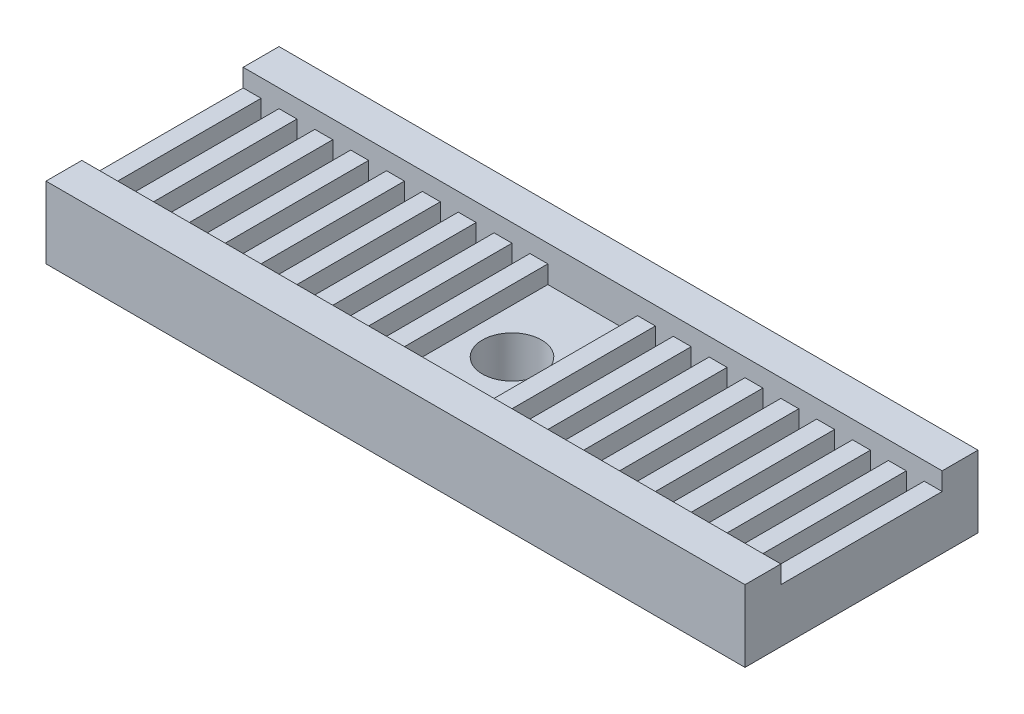
SolidWorks part; units mm, degrees
ref_plane "Front Plane" through (0, 0, 0) normal (0, 0, 1) x (1, 0, 0)
ref_plane "Top Plane" through (0, 0, 0) normal (0, 1, 0) x (1, 0, 0)
ref_plane "Right Plane" through (0, 0, 0) normal (1, 0, 0) x (0, 0, -1)
sketch "Sketch1" plane through (0, 0, 0) normal (0, 1, 0) x (1, 0, 0)
  line L5 (-19.5, -6.5) -> (19.5, -6.5)
  line L6 (-19.5, -6.5) -> (-19.5, 6.5)
  line L15 (-19.5, 6.5) -> (19.5, 6.5)
  line L16 (19.5, -6.5) -> (19.5, 6.5)
  line L17 (-19.5, -6.5) -> (19.5, 6.5) construction
  line L18 (-19.5, 6.5) -> (19.5, -6.5) construction
  point P0 (0, 0)
  dimension "D1" = 13
  dimension "D2" = 39
extrude "Boss-Extrude1" add sketch "Sketch1" along normal blind 5
sketch "Sketch5" plane through (0, 5, 0) normal (0, 1, 0) x (1, 0, 0)
  line L5 (19.5, -6.5) -> (19.5, 6.5) construction
  line L6 (-19.5, -4.5) -> (19.5, -4.5)
  line L8 (-19.5, -4.5) -> (-19.5, 4.5)
  line L9 (-19.5, 4.5) -> (19.5, 4.5)
  line L10 (19.5, -4.5) -> (19.5, 4.5)
  line L11 (-19.5, -4.5) -> (19.5, 4.5) construction
  line L12 (-19.5, 4.5) -> (19.5, -4.5) construction
  point P0 (0, 0)
  dimension "D1" = 9
extrude "Cut-Extrude1" cut sketch "Sketch5" against normal blind 2
sketch "Sketch2" plane through (0, 3, 0) normal (0, 1, 0) x (1, 0, 0)
  line L0 (-19.5, 0) -> (19.5, 0) construction
  line L1 (6.5, -4.5) -> (6.5, 4.5)
  line L2 (6.5, -4.5) -> (5.5, -4.5)
  line L3 (-17.5, -4.5) -> (-17.5, 4.5)
  line L4 (-18.5, -4.5) -> (-19.5, -4.5)
  line L5 (-18.5, -4.5) -> (-18.5, 4.5)
  line L6 (-18.5, 4.5) -> (-19.5, 4.5)
  line L7 (-19.5, -4.5) -> (-19.5, 4.5)
  line L8 (-18.5, -4.5) -> (-19.5, 4.5) construction
  line L9 (-18.5, 4.5) -> (-19.5, -4.5) construction
  line L10 (-17.5, -4.5) -> (-18.5, -4.5)
  line L11 (-18.5, -4.5) -> (-18.5, 4.5)
  line L12 (-17.5, 4.5) -> (-18.5, 4.5)
  line L13 (-16.5, -4.5) -> (-16.5, 4.5)
  line L14 (-16.5, -4.5) -> (-17.5, -4.5)
  line L15 (-17.5, -4.5) -> (-17.5, 4.5)
  line L16 (-16.5, 4.5) -> (-17.5, 4.5)
  line L17 (-15.5, -4.5) -> (-15.5, 4.5)
  line L18 (-15.5, -4.5) -> (-16.5, -4.5)
  line L19 (-16.5, -4.5) -> (-16.5, 4.5)
  line L20 (-15.5, 4.5) -> (-16.5, 4.5)
  line L21 (-14.5, -4.5) -> (-14.5, 4.5)
  line L22 (-14.5, -4.5) -> (-15.5, -4.5)
  line L23 (-15.5, -4.5) -> (-15.5, 4.5)
  line L24 (-14.5, 4.5) -> (-15.5, 4.5)
  line L25 (-13.5, -4.5) -> (-13.5, 4.5)
  line L26 (-13.5, -4.5) -> (-14.5, -4.5)
  line L27 (-14.5, -4.5) -> (-14.5, 4.5)
  line L28 (-13.5, 4.5) -> (-14.5, 4.5)
  line L29 (-12.5, -4.5) -> (-12.5, 4.5)
  line L30 (-12.5, -4.5) -> (-13.5, -4.5)
  line L31 (-13.5, -4.5) -> (-13.5, 4.5)
  line L32 (-12.5, 4.5) -> (-13.5, 4.5)
  line L33 (-11.5, -4.5) -> (-11.5, 4.5)
  line L34 (-11.5, -4.5) -> (-12.5, -4.5)
  line L35 (-12.5, -4.5) -> (-12.5, 4.5)
  line L36 (-11.5, 4.5) -> (-12.5, 4.5)
  line L37 (-10.5, -4.5) -> (-10.5, 4.5)
  line L38 (-10.5, -4.5) -> (-11.5, -4.5)
  line L39 (-11.5, -4.5) -> (-11.5, 4.5)
  line L40 (-10.5, 4.5) -> (-11.5, 4.5)
  line L41 (-9.5, -4.5) -> (-9.5, 4.5)
  line L42 (-9.5, -4.5) -> (-10.5, -4.5)
  line L43 (-10.5, -4.5) -> (-10.5, 4.5)
  line L44 (-9.5, 4.5) -> (-10.5, 4.5)
  line L45 (-8.5, -4.5) -> (-8.5, 4.5)
  line L46 (-8.5, -4.5) -> (-9.5, -4.5)
  line L47 (-9.5, -4.5) -> (-9.5, 4.5)
  line L48 (-8.5, 4.5) -> (-9.5, 4.5)
  line L49 (-7.5, -4.5) -> (-7.5, 4.5)
  line L50 (-7.5, -4.5) -> (-8.5, -4.5)
  line L51 (-8.5, -4.5) -> (-8.5, 4.5)
  line L52 (-7.5, 4.5) -> (-8.5, 4.5)
  line L53 (-6.5, -4.5) -> (-6.5, 4.5)
  line L54 (-6.5, -4.5) -> (-7.5, -4.5)
  line L55 (-7.5, -4.5) -> (-7.5, 4.5)
  line L56 (-6.5, 4.5) -> (-7.5, 4.5)
  line L57 (-5.5, -4.5) -> (-5.5, 4.5)
  line L58 (-5.5, -4.5) -> (-6.5, -4.5)
  line L59 (-6.5, -4.5) -> (-6.5, 4.5)
  line L60 (-5.5, 4.5) -> (-6.5, 4.5)
  line L61 (-4.5, -4.5) -> (-4.5, 4.5)
  line L62 (-4.5, -4.5) -> (-5.5, -4.5)
  line L63 (-5.5, -4.5) -> (-5.5, 4.5)
  line L64 (-4.5, 4.5) -> (-5.5, 4.5)
  line L65 (-3.5, -4.5) -> (-3.5, 4.5)
  line L66 (-3.5, -4.5) -> (-4.5, -4.5)
  line L67 (-4.5, -4.5) -> (-4.5, 4.5)
  line L68 (-3.5, 4.5) -> (-4.5, 4.5)
  line L69 (-2.5, -4.5) -> (-2.5, 4.5)
  line L70 (-2.5, -4.5) -> (-3.5, -4.5)
  line L71 (-3.5, -4.5) -> (-3.5, 4.5)
  line L72 (-2.5, 4.5) -> (-3.5, 4.5)
  line L73 (-1.5, -4.5) -> (-1.5, 4.5)
  line L74 (-1.5, -4.5) -> (-2.5, -4.5)
  line L75 (-2.5, -4.5) -> (-2.5, 4.5)
  line L76 (-1.5, 4.5) -> (-2.5, 4.5)
  line L77 (-0.5, -4.5) -> (-0.5, 4.5)
  line L78 (-0.5, -4.5) -> (-1.5, -4.5)
  line L79 (-1.5, -4.5) -> (-1.5, 4.5)
  line L80 (-0.5, 4.5) -> (-1.5, 4.5)
  line L81 (0.5, -4.5) -> (0.5, 4.5)
  line L82 (0.5, -4.5) -> (-0.5, -4.5)
  line L83 (-0.5, -4.5) -> (-0.5, 4.5)
  line L84 (0.5, 4.5) -> (-0.5, 4.5)
  line L85 (1.5, -4.5) -> (1.5, 4.5)
  line L86 (1.5, -4.5) -> (0.5, -4.5)
  line L87 (0.5, -4.5) -> (0.5, 4.5)
  line L88 (1.5, 4.5) -> (0.5, 4.5)
  line L89 (2.5, -4.5) -> (2.5, 4.5)
  line L90 (2.5, -4.5) -> (1.5, -4.5)
  line L91 (1.5, -4.5) -> (1.5, 4.5)
  line L92 (2.5, 4.5) -> (1.5, 4.5)
  line L93 (3.5, -4.5) -> (3.5, 4.5)
  line L94 (3.5, -4.5) -> (2.5, -4.5)
  line L95 (2.5, -4.5) -> (2.5, 4.5)
  line L96 (3.5, 4.5) -> (2.5, 4.5)
  line L97 (4.5, -4.5) -> (4.5, 4.5)
  line L98 (4.5, -4.5) -> (3.5, -4.5)
  line L99 (3.5, -4.5) -> (3.5, 4.5)
  line L100 (4.5, 4.5) -> (3.5, 4.5)
  line L101 (5.5, -4.5) -> (5.5, 4.5)
  line L102 (5.5, -4.5) -> (4.5, -4.5)
  line L103 (4.5, -4.5) -> (4.5, 4.5)
  line L104 (5.5, 4.5) -> (4.5, 4.5)
  line L105 (5.5, -4.5) -> (5.5, 4.5)
  line L106 (-19.5, 4.5) -> (-19.5, -4.5) construction
  line L107 (6.5, 4.5) -> (5.5, 4.5)
  line L108 (7.5, -4.5) -> (7.5, 4.5)
  line L109 (7.5, -4.5) -> (6.5, -4.5)
  line L110 (6.5, -4.5) -> (6.5, 4.5)
  line L111 (7.5, 4.5) -> (6.5, 4.5)
  line L112 (8.5, -4.5) -> (8.5, 4.5)
  line L113 (8.5, -4.5) -> (7.5, -4.5)
  line L114 (7.5, -4.5) -> (7.5, 4.5)
  line L115 (8.5, 4.5) -> (7.5, 4.5)
  line L116 (9.5, -4.5) -> (9.5, 4.5)
  line L117 (9.5, -4.5) -> (8.5, -4.5)
  line L118 (8.5, -4.5) -> (8.5, 4.5)
  line L119 (9.5, 4.5) -> (8.5, 4.5)
  line L120 (10.5, -4.5) -> (10.5, 4.5)
  line L121 (10.5, -4.5) -> (9.5, -4.5)
  line L122 (9.5, -4.5) -> (9.5, 4.5)
  line L123 (10.5, 4.5) -> (9.5, 4.5)
  line L124 (11.5, -4.5) -> (11.5, 4.5)
  line L125 (11.5, -4.5) -> (10.5, -4.5)
  line L126 (10.5, -4.5) -> (10.5, 4.5)
  line L127 (11.5, 4.5) -> (10.5, 4.5)
  line L128 (12.5, -4.5) -> (12.5, 4.5)
  line L129 (12.5, -4.5) -> (11.5, -4.5)
  line L130 (11.5, -4.5) -> (11.5, 4.5)
  line L131 (12.5, 4.5) -> (11.5, 4.5)
  line L132 (13.5, -4.5) -> (13.5, 4.5)
  line L133 (13.5, -4.5) -> (12.5, -4.5)
  line L134 (12.5, -4.5) -> (12.5, 4.5)
  line L135 (13.5, 4.5) -> (12.5, 4.5)
  line L136 (14.5, -4.5) -> (14.5, 4.5)
  line L137 (14.5, -4.5) -> (13.5, -4.5)
  line L138 (13.5, -4.5) -> (13.5, 4.5)
  line L139 (14.5, 4.5) -> (13.5, 4.5)
  line L140 (15.5, -4.5) -> (15.5, 4.5)
  line L141 (15.5, -4.5) -> (14.5, -4.5)
  line L142 (14.5, -4.5) -> (14.5, 4.5)
  line L143 (15.5, 4.5) -> (14.5, 4.5)
  line L144 (16.5, -4.5) -> (16.5, 4.5)
  line L145 (16.5, -4.5) -> (15.5, -4.5)
  line L146 (15.5, -4.5) -> (15.5, 4.5)
  line L147 (16.5, 4.5) -> (15.5, 4.5)
  line L148 (17.5, -4.5) -> (17.5, 4.5)
  line L149 (17.5, -4.5) -> (16.5, -4.5)
  line L150 (16.5, -4.5) -> (16.5, 4.5)
  line L151 (17.5, 4.5) -> (16.5, 4.5)
  line L152 (18.5, -4.5) -> (18.5, 4.5)
  line L153 (18.5, -4.5) -> (17.5, -4.5)
  line L154 (17.5, -4.5) -> (17.5, 4.5)
  line L155 (18.5, 4.5) -> (17.5, 4.5)
  line L156 (19.5, -4.5) -> (19.5, 4.5)
  line L157 (19.5, -4.5) -> (18.5, -4.5)
  line L158 (18.5, -4.5) -> (18.5, 4.5)
  line L159 (19.5, 4.5) -> (18.5, 4.5)
  line L160 (20.5, -4.5) -> (20.5, 4.5)
  line L161 (20.5, -4.5) -> (19.5, -4.5)
  line L162 (19.5, -4.5) -> (19.5, 4.5)
  line L163 (20.5, 4.5) -> (19.5, 4.5)
  line L164 (19.5, -4.5) -> (19.5, 4.5) construction
  point P6 (-19, 0)
  dimension "D1" = 1
  dimension "D2" = 9
  dimension "D3" = 40
extrude "Boss-Extrude2" add sketch "Sketch2" along normal blind 1
sketch "Sketch6" plane through (0, 0, 0) normal (0, -1, 0) x (1, 0, 0)
  circle A0 centre (0, 0) radius 1.65
  dimension "D1" = 3.3
extrude "Cut-Extrude2" cut sketch "Sketch6" against normal through all
chamfer "Chamfer1" distance 1 angle 45 4 edges at (-19.5, 0, 0) (0, 0, 6.5) (19.5, 0, 0) (0, 0, -6.5)
